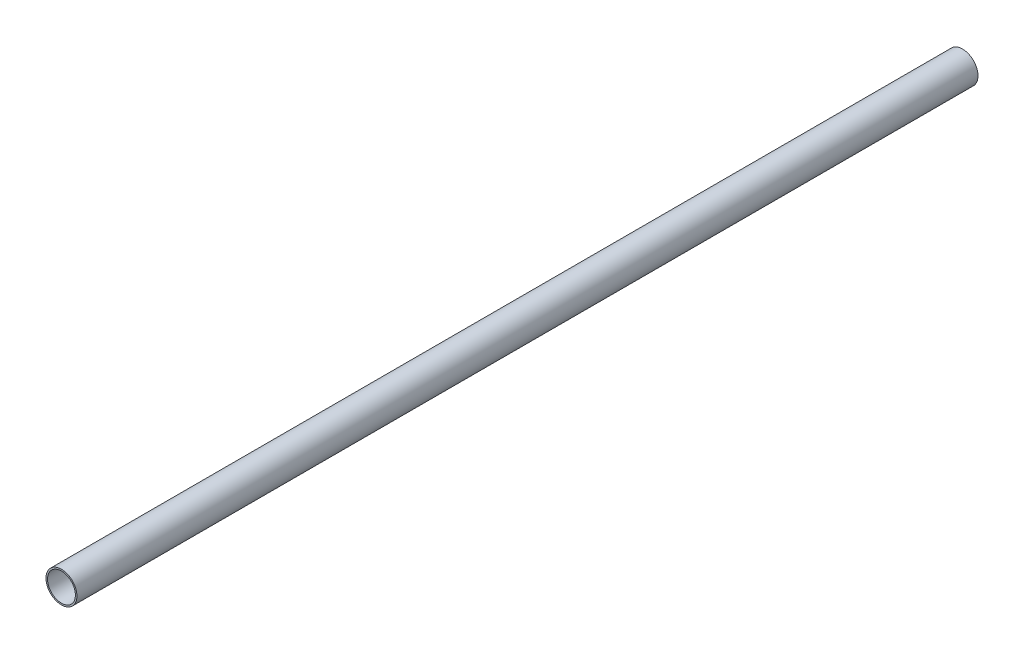
SolidWorks part; units mm, degrees
material "Beryllium Copper, UNS C17200"
ref_plane "Front Plane" through (0, 0, 0) normal (0, 0, 1) x (1, 0, 0)
ref_plane "Top Plane" through (0, 0, 0) normal (0, 1, 0) x (1, 0, 0)
ref_plane "Right Plane" through (0, 0, 0) normal (1, 0, 0) x (0, 0, -1)
sketch "Sketch1" plane through (0, 0, 0) normal (0, 0, 1) x (1, 0, 0)
  circle A0 centre (0, 0) radius 5
  dimension "D1" = 10
extrude "Extrude-Thin1" add sketch "Sketch1" against normal blind 291 thin thin type one direction reverse wall 0.5
